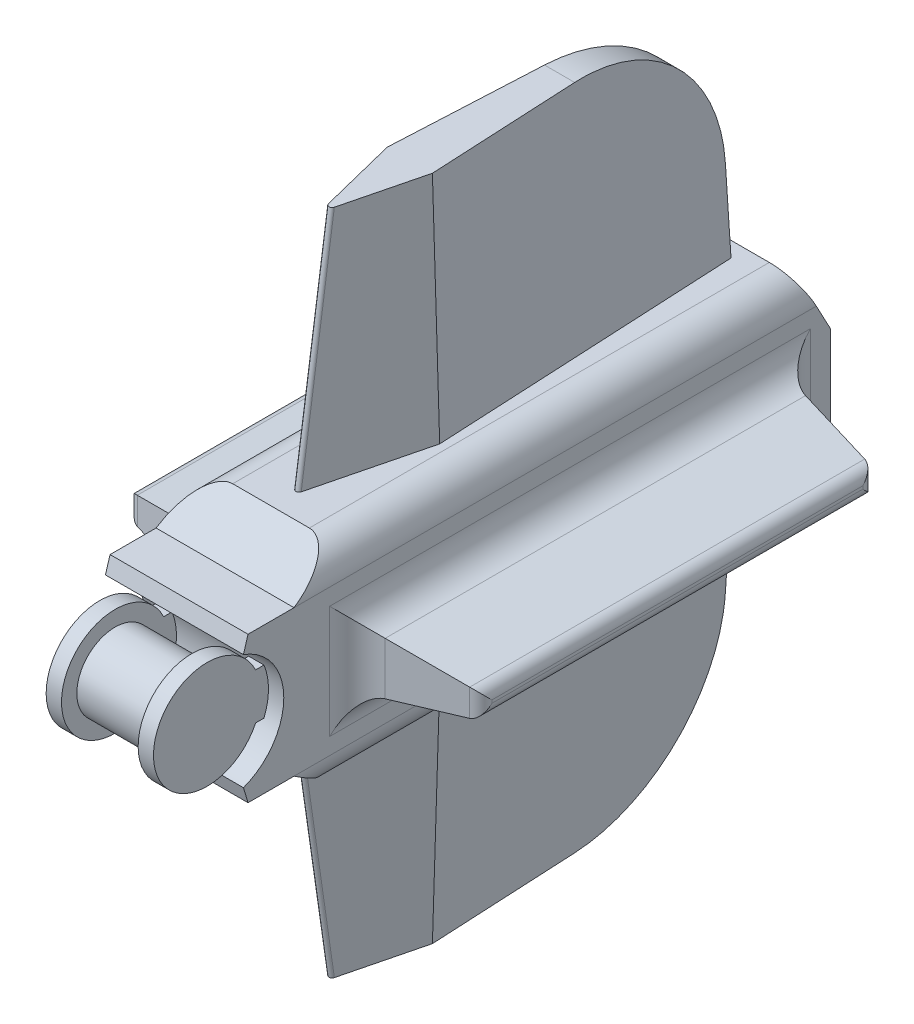
SolidWorks part; units mm, degrees
ref_plane "Front Plane" through (0, 0, 0) normal (0, 0, 1) x (1, 0, 0)
ref_plane "Top Plane" through (0, 0, 0) normal (0, 1, 0) x (1, 0, 0)
ref_plane "Right Plane" through (0, 0, 0) normal (1, 0, 0) x (0, 0, -1)
sketch "Sketch1" plane through (0, 0, 0) normal (1, 0, 0) x (0, 0, -1)
  circle A0 centre (0, 0) radius 3.175
  dimension "D1" = 6.35
extrude "Boss-Extrude1" add sketch "Sketch1" along normal mid plane 6.35
sketch "Sketch2" plane through (3.175, 0, 0) normal (1, 0, 0) x (0, 0, -1)
  circle A0 centre (0, 0) radius 4.445
  dimension "D1" = 8.89
extrude "Boss-Extrude2" add sketch "Sketch2" along normal blind 1.27
mirror "Mirror1" about plane through (0, 0, 0) normal (1, 0, 0) of "Boss-Extrude2"
sketch "Sketch3" plane through (4.445, 0, 0) normal (1, 0, 0) x (0, 0, -1)
  line L1 (0, 1.905) -> (6.35, 1.905)
  line L2 (0, 1.905) -> (0, -1.905)
  line L3 (0, -1.905) -> (6.35, -1.905)
  line L4 (6.35, 1.905) -> (6.35, -1.905)
  point P4 (0, 0)
  dimension "D1" = 3.81
  dimension "D2" = 6.35
extrude "Boss-Extrude3" add sketch "Sketch3" against normal blind 1.27
mirror "Mirror2" about plane through (0, 0, 0) normal (1, 0, 0) of "Boss-Extrude3"
sketch "Sketch4" plane through (-3.175, 0, 0) normal (1, 0, 0) x (0, 0, -1)
  line L0 (1.7375, 4.7736) -> (0, 0) construction
  line L1 (0, 0) -> (5.08, 0) construction
  line L2 (1.7375, 4.7736) -> (2.1185, 6.0436)
  line L3 (2.1185, 6.0436) -> (5.9285, 6.0436)
  line L4 (0, 0) -> (1.7375, -4.7736) construction
  line L5 (5.9285, 6.0436) -> (9.7385, 8.5836)
  line L6 (9.7385, 8.5836) -> (47.8385, 8.5836)
  line L7 (47.8385, 8.5836) -> (50.3785, 3.81)
  line L8 (50.3785, 3.81) -> (50.3785, -3.81)
  line L9 (50.3785, 0) -> (5.08, 0) construction
  line L10 (47.8385, -8.5836) -> (50.3785, -3.81)
  line L11 (9.7385, -8.5836) -> (47.8385, -8.5836)
  line L12 (5.9285, -6.0436) -> (9.7385, -8.5836)
  line L13 (2.1185, -6.0436) -> (5.9285, -6.0436)
  line L14 (1.7375, -4.7736) -> (2.1185, -6.0436)
  arc A0 (1.7375, 4.7736) -> (1.7375, -4.7736) centre (0, 0) cw
  dimension "D1" = 5.08
  dimension "D2" = 140
  dimension "D3" = 1.27
  dimension "D4" = 0.381
  dimension "D5" = 3.81
  dimension "D6" = 3.81
  dimension "D7" = 2.54
  dimension "D8" = 38.1
  dimension "D9" = 7.62
  dimension "D10" = 2.54
extrude "Boss-Extrude4" add sketch "Sketch4" against normal blind 2.54 and the other way blind 8.89
sketch "Sketch5" plane through (0, 0, -50.3785) normal (0, 0, -1) x (-1, 0, 0)
  circle A0 centre (0, 0) radius 3.175
  dimension "D1" = 6.35
extrude "Cut-Extrude1" cut sketch "Sketch5" against normal blind 12.7
fillet "Fillet1" radius 2.54 4 edges at (5.715, -8.5836, -28.7885) (-5.715, -8.5836, -28.7885) (-5.715, 8.5836, -28.7885) (5.715, 8.5836, -28.7885)
sketch "Sketch6" plane through (5.715, 0, 0) normal (1, 0, 0) x (0, 0, -1)
  line L0 (50.3785, -3.81) -> (50.3785, 3.81) construction
  line L1 (11.0085, 2.54) -> (46.5685, 2.54)
  line L2 (11.0085, 2.54) -> (11.0085, -2.54)
  line L3 (11.0085, -2.54) -> (46.5685, -2.54)
  line L4 (46.5685, 2.54) -> (46.5685, -2.54)
  point P4 (11.0085, 0)
  point P6 (50.3785, 0)
  dimension "D1" = 3.81
  dimension "D2" = 5.08
  dimension "D3" = 35.56
extrude "Boss-Extrude5" add sketch "Sketch6" along normal blind 8.89 draft 10
mirror "Mirror3" about plane through (0, 0, 0) normal (1, 0, 0) of "Boss-Extrude5"
fillet "Fillet2" radius 1.016 8 edges at (-14.605, -0.9725, -28.7885) (-14.605, 0, -45.0009) (-14.605, 0.9725, -28.7885) (-14.605, 0, -12.576) (14.605, 0.9725, -28.7885) (14.605, 0, -45.0009) (14.605, -0.9725, -28.7885) (14.605, 0, -12.576)
fillet "Fillet3" radius 2.54 8 edges at (5.715, -2.54, -28.7885) (5.715, 0, -11.0085) (5.715, 0, -46.5685) (5.715, 2.54, -28.7885) (-5.715, 0, -11.0085) (-5.715, 0, -46.5685) (-5.715, -2.54, -28.7885) (-5.715, 2.54, -28.7885)
sketch "Sketch7" plane through (0, 8.5836, 0) normal (0, 1, 0) x (1, 0, 0)
  line L0 (0, 9.7385) -> (0, 47.8385) construction
  line L1 (3.175, 9.7385) -> (-3.175, 9.7385) construction
  line L2 (3.175, 47.8385) -> (-3.175, 47.8385) construction
  line L3 (-1.27, 46.5685) -> (1.27, 46.5685)
  line L4 (1.27, 46.5685) -> (2.54, 21.1685)
  line L5 (2.54, 21.1685) -> (0, 11.0085)
  line L6 (0, 11.0085) -> (-2.54, 21.1685)
  line L7 (-2.54, 21.1685) -> (-1.27, 46.5685)
  point P8 (0, 46.5685)
  dimension "D1" = 2.54
  dimension "D2" = 1.27
  dimension "D3" = 1.27
  dimension "D4" = 2.54
  dimension "D5" = 25.4
extrude "Boss-Extrude6" add sketch "Sketch7" along normal blind 19.05 draft 2
mirror "Mirror4" about plane through (0, 0, 0) normal (0, 1, 0) of "Boss-Extrude6"
fillet "Fillet4" radius 0.254 2 edges at (0, -18.1086, -12.3799) (0, 18.1086, -12.3799)
fillet "Fillet5" radius 12.7 2 edges at (0, -27.6336, -45.9032) (0, 27.6336, -45.9032)
